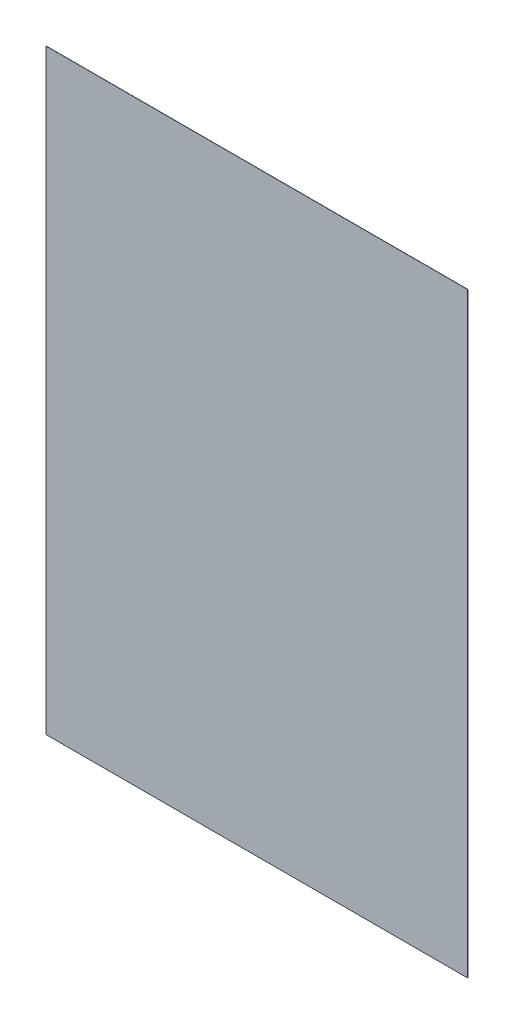
SolidWorks part; units mm, degrees
ref_plane "Front" through (0, 0, 0) normal (0, 0, 1) x (1, 0, 0)
ref_plane "Top" through (0, 0, 0) normal (0, 1, 0) x (1, 0, 0)
ref_plane "Right" through (0, 0, 0) normal (1, 0, 0) x (0, 0, -1)
sketch "Sketch1" plane through (0, 0, 0) normal (0, 0, 1) x (1, 0, 0)
  line L0 (0, 0) -> (210, 0)
  line L1 (0, 0) -> (0, 297)
  line L2 (210, 0) -> (210, 297)
  line L3 (0, 297) -> (210, 297)
  dimension "D1" = 210
  dimension "D2" = 297
extrude "Boss-Extrude1" add sketch "Sketch1" along normal blind 0.1
